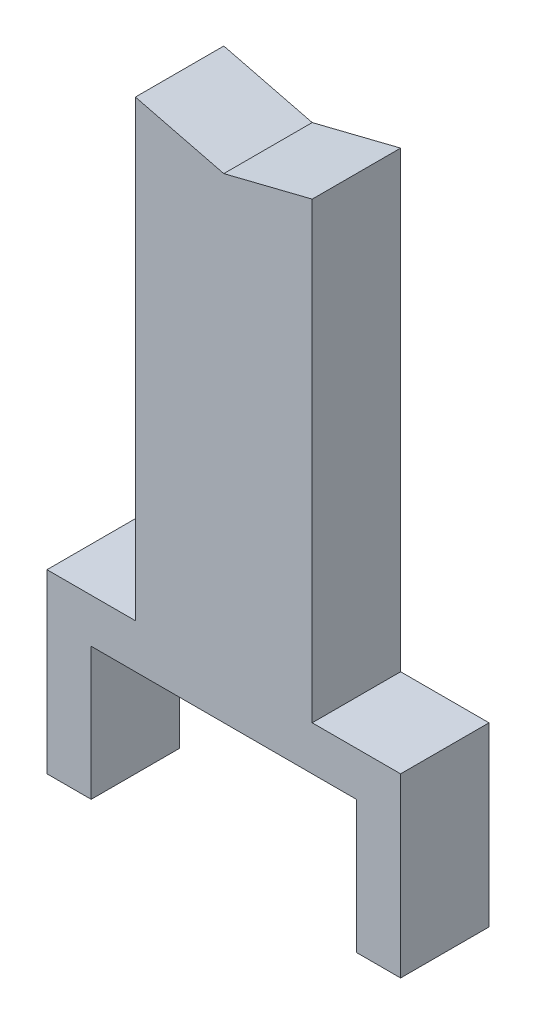
SolidWorks part; units mm, degrees
ref_plane "Front Plane" through (0, 0, 0) normal (0, 0, 1) x (1, 0, 0)
ref_plane "Top Plane" through (0, 0, 0) normal (0, 1, 0) x (1, 0, 0)
ref_plane "Right Plane" through (0, 0, 0) normal (1, 0, 0) x (0, 0, -1)
sketch "Sketch1" plane through (0, 0, 0) normal (0, 0, 1) x (1, 0, 0)
  line L0 (-50.8, 362.204) -> (0, 349.504)
  line L2 (-50.8, 101.6) -> (-50.8, 362.204)
  line L4 (50.8, 101.6) -> (50.8, 362.204)
  line L5 (0, 349.504) -> (50.8, 362.204)
  line L6 (0, 402.6876) -> (0, 0) construction
  line L11 (-76.2, 0) -> (-76.2, 76.2)
  line L12 (-76.2, 76.2) -> (0, 76.2)
  line L13 (-76.2, 0) -> (-101.6, 0)
  line L14 (-101.6, 0) -> (-101.6, 101.6)
  line L15 (-101.6, 101.6) -> (-50.8, 101.6)
  line L17 (101.6, 101.6) -> (50.8, 101.6)
  line L18 (101.6, 0) -> (101.6, 101.6)
  line L19 (76.2, 0) -> (101.6, 0)
  line L20 (76.2, 0) -> (76.2, 76.2)
  line L21 (76.2, 76.2) -> (0, 76.2)
  point P0 (-76.2, 38.1)
  dimension "D1" = 203.2
  dimension "D2" = 101.6
  dimension "D3" = 12.7
  dimension "D4" = 101.6
  dimension "D5" = 25.4
  dimension "D6" = 25.4
  dimension "D7" = 362.204
extrude "Boss-Extrude1" add sketch "Sketch1" along normal mid plane 50.8
